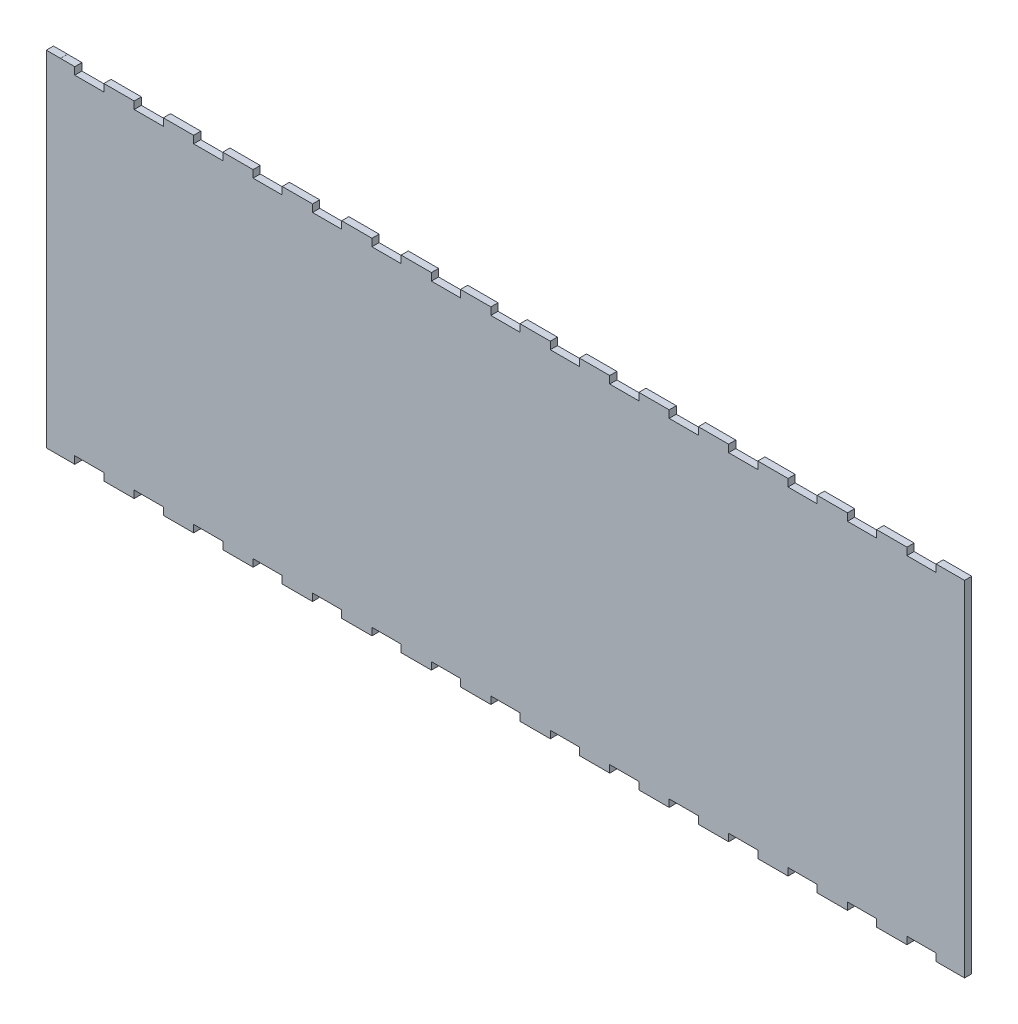
SolidWorks part; units mm, degrees
ref_plane "Front Plane" through (0, 0, 0) normal (0, 0, 1) x (1, 0, 0)
ref_plane "Top Plane" through (0, 0, 0) normal (0, 1, 0) x (1, 0, 0)
ref_plane "Right Plane" through (0, 0, 0) normal (1, 0, 0) x (0, 0, -1)
sketch "Sketch1" plane through (0, 0, 0) normal (0, 0, 1) x (1, 0, 0)
  line L252 (393.8, 152.4) -> (393.8, 149.125)
  line L253 (393.8, 149.125) -> (380.9, 149.125)
  line L254 (380.9, 149.125) -> (380.9, 152.4)
  line L255 (380.9, 152.4) -> (367.4929, 152.4)
  line L256 (367.4929, 152.4) -> (367.4929, 149.125)
  line L257 (367.4929, 149.125) -> (354.5929, 149.125)
  line L258 (354.5929, 149.125) -> (354.5929, 152.4)
  line L259 (354.5929, 152.4) -> (341.1857, 152.4)
  line L260 (341.1857, 152.4) -> (341.1857, 149.125)
  line L261 (341.1857, 149.125) -> (328.2857, 149.125)
  line L262 (328.2857, 149.125) -> (328.2857, 152.4)
  line L263 (328.2857, 152.4) -> (314.8786, 152.4)
  line L264 (314.8786, 152.4) -> (314.8786, 149.125)
  line L265 (314.8786, 149.125) -> (301.9786, 149.125)
  line L266 (301.9786, 149.125) -> (301.9786, 152.4)
  line L267 (301.9786, 152.4) -> (288.5714, 152.4)
  line L268 (288.5714, 152.4) -> (288.5714, 149.125)
  line L269 (288.5714, 149.125) -> (275.6714, 149.125)
  line L270 (275.6714, 149.125) -> (275.6714, 152.4)
  line L271 (275.6714, 152.4) -> (262.2643, 152.4)
  line L272 (262.2643, 152.4) -> (262.2643, 149.125)
  line L273 (262.2643, 149.125) -> (249.3643, 149.125)
  line L274 (249.3643, 149.125) -> (249.3643, 152.4)
  line L275 (249.3643, 152.4) -> (235.9571, 152.4)
  line L276 (235.9571, 152.4) -> (235.9571, 149.125)
  line L277 (235.9571, 149.125) -> (223.0571, 149.125)
  line L278 (223.0571, 149.125) -> (223.0571, 152.4)
  line L279 (223.0571, 152.4) -> (209.65, 152.4)
  line L280 (209.65, 152.4) -> (209.65, 149.125)
  line L281 (209.65, 149.125) -> (196.75, 149.125)
  line L282 (196.75, 149.125) -> (196.75, 152.4)
  line L283 (196.75, 152.4) -> (183.3429, 152.4)
  line L284 (183.3429, 152.4) -> (183.3429, 149.125)
  line L285 (183.3429, 149.125) -> (170.4429, 149.125)
  line L286 (170.4429, 149.125) -> (170.4429, 152.4)
  line L287 (170.4429, 152.4) -> (157.0357, 152.4)
  line L288 (157.0357, 152.4) -> (157.0357, 149.125)
  line L289 (157.0357, 149.125) -> (144.1357, 149.125)
  line L290 (144.1357, 149.125) -> (144.1357, 152.4)
  line L291 (144.1357, 152.4) -> (130.7286, 152.4)
  line L292 (130.7286, 152.4) -> (130.7286, 149.125)
  line L293 (130.7286, 149.125) -> (117.8286, 149.125)
  line L294 (117.8286, 149.125) -> (117.8286, 152.4)
  line L295 (117.8286, 152.4) -> (104.4214, 152.4)
  line L296 (104.4214, 152.4) -> (104.4214, 149.125)
  line L297 (104.4214, 149.125) -> (91.5214, 149.125)
  line L298 (91.5214, 149.125) -> (91.5214, 152.4)
  line L299 (91.5214, 152.4) -> (78.1143, 152.4)
  line L300 (78.1143, 152.4) -> (78.1143, 149.125)
  line L301 (78.1143, 149.125) -> (65.2143, 149.125)
  line L302 (65.2143, 149.125) -> (65.2143, 152.4)
  line L303 (65.2143, 152.4) -> (51.8071, 152.4)
  line L304 (51.8071, 152.4) -> (51.8071, 149.125)
  line L305 (51.8071, 149.125) -> (38.9071, 149.125)
  line L306 (38.9071, 149.125) -> (38.9071, 152.4)
  line L307 (38.9071, 152.4) -> (25.5, 152.4)
  line L308 (25.5, 152.4) -> (25.5, 149.125)
  line L309 (25.5, 149.125) -> (12.6, 149.125)
  line L310 (12.6, 149.125) -> (12.6, 152.4)
  line L311 (12.6, 152.4) -> (6.25, 152.4)
  line L312 (6.25, 152.4) -> (6.25, 152.4254)
  line L313 (6.25, 152.4254) -> (0, 152.4254)
  line L314 (0, 152.4254) -> (0, -0.0254)
  line L315 (0, -0.0254) -> (12.6, -0.0254)
  line L316 (12.6, -0.0254) -> (12.6, 3.275)
  line L317 (12.6, 3.275) -> (25.5, 3.275)
  line L318 (25.5, 3.275) -> (25.5, 0)
  line L319 (25.5, 0) -> (38.9071, 0)
  line L320 (38.9071, 0) -> (38.9071, 3.275)
  line L321 (38.9071, 3.275) -> (51.8071, 3.275)
  line L322 (51.8071, 3.275) -> (51.8071, 0)
  line L323 (51.8071, 0) -> (65.2143, 0)
  line L324 (65.2143, 0) -> (65.2143, 3.275)
  line L325 (65.2143, 3.275) -> (78.1143, 3.275)
  line L326 (78.1143, 3.275) -> (78.1143, 0)
  line L327 (78.1143, 0) -> (91.5214, 0)
  line L328 (91.5214, 0) -> (91.5214, 3.275)
  line L329 (91.5214, 3.275) -> (104.4214, 3.275)
  line L330 (104.4214, 3.275) -> (104.4214, 0)
  line L331 (104.4214, 0) -> (117.8286, 0)
  line L332 (117.8286, 0) -> (117.8286, 3.275)
  line L333 (117.8286, 3.275) -> (130.7286, 3.275)
  line L334 (130.7286, 3.275) -> (130.7286, 0)
  line L335 (130.7286, 0) -> (144.1357, 0)
  line L336 (144.1357, 0) -> (144.1357, 3.275)
  line L337 (144.1357, 3.275) -> (157.0357, 3.275)
  line L338 (157.0357, 3.275) -> (157.0357, 0)
  line L339 (157.0357, 0) -> (170.4429, 0)
  line L340 (170.4429, 0) -> (170.4429, 3.275)
  line L341 (170.4429, 3.275) -> (183.3429, 3.275)
  line L342 (183.3429, 3.275) -> (183.3429, 0)
  line L343 (183.3429, 0) -> (196.75, 0)
  line L344 (196.75, 0) -> (196.75, 3.275)
  line L345 (196.75, 3.275) -> (209.65, 3.275)
  line L346 (209.65, 3.275) -> (209.65, 0)
  line L347 (209.65, 0) -> (223.0571, 0)
  line L348 (223.0571, 0) -> (223.0571, 3.275)
  line L349 (223.0571, 3.275) -> (235.9571, 3.275)
  line L350 (235.9571, 3.275) -> (235.9571, 0)
  line L351 (235.9571, 0) -> (249.3643, 0)
  line L352 (249.3643, 0) -> (249.3643, 3.275)
  line L353 (249.3643, 3.275) -> (262.2643, 3.275)
  line L354 (262.2643, 3.275) -> (262.2643, 0)
  line L355 (262.2643, 0) -> (275.6714, 0)
  line L356 (275.6714, 0) -> (275.6714, 3.275)
  line L357 (275.6714, 3.275) -> (288.5714, 3.275)
  line L358 (288.5714, 3.275) -> (288.5714, 0)
  line L359 (288.5714, 0) -> (301.9786, 0)
  line L360 (301.9786, 0) -> (301.9786, 3.275)
  line L361 (301.9786, 3.275) -> (314.8786, 3.275)
  line L362 (314.8786, 3.275) -> (314.8786, 0)
  line L363 (314.8786, 0) -> (328.2857, 0)
  line L364 (328.2857, 0) -> (328.2857, 3.275)
  line L365 (328.2857, 3.275) -> (341.1857, 3.275)
  line L366 (341.1857, 3.275) -> (341.1857, 0)
  line L367 (341.1857, 0) -> (354.5929, 0)
  line L368 (354.5929, 0) -> (354.5929, 3.275)
  line L369 (354.5929, 3.275) -> (367.4929, 3.275)
  line L370 (367.4929, 3.275) -> (367.4929, 0)
  line L371 (367.4929, 0) -> (380.9, 0)
  line L372 (380.9, 0) -> (380.9, 3.275)
  line L373 (380.9, 3.275) -> (393.8, 3.275)
  line L374 (393.8, 3.275) -> (393.8, 0)
  line L375 (393.8, 0) -> (406.4, 0)
  line L376 (406.4, 0) -> (406.4, 152.4)
  line L377 (406.4, 152.4) -> (393.8, 152.4)
extrude "Boss-Extrude2" add sketch "Sketch1" along normal blind 3.175 contours L314 L315 L316 L317 L318 L319 L320 L321 L322 L323 L324 L325 L326 L327 L328 L329 L330 L331 L332 L333 L334 L335 L336 L337 L338 L339 L340 L341 L342 L343 L344 L345 L346 L347 L348 L349 L350 L351 L352 L353 L354 L355 L356 L357 L358 L359 L360 L361 L362 L363 L364 L365 L366 L367 L368 L369 L370 L371 L372 L373 L374 L375 L376 L377 L252 L253 L254 L255 L256 L257 L258 L259 L260 L261 L262 L263 L264 L265 L266 L267 L268 L269 L270 L271 L272 L273 L274 L275 L276 L277 L278 L279 L280 L281 L282 L283 L284 L285 L286 L287 L288 L289 L290 L291 L292 L293 L294 L295 L296 L297 L298 L299 L300 L301 L302 L303 L304 L305 L306 L307 L308 L309 L310 L311 L312 L313
sketch "DXF" plane through (0, 0, 3.175) normal (0, 0, 1) x (1, 0, 0)
  line L252 (6.3516, 152.527) -> (-0.1016, 152.527)
  line L253 (-0.1016, 152.527) -> (-0.1016, -0.127)
  line L254 (-0.1016, -0.127) -> (12.7016, -0.127)
  line L255 (12.7016, -0.127) -> (12.7016, 3.1734)
  line L256 (12.7016, 3.1734) -> (25.3984, 3.1734)
  line L257 (25.3984, 3.1734) -> (25.3984, -0.1016)
  line L258 (25.3984, -0.1016) -> (39.0087, -0.1016)
  line L259 (39.0087, -0.1016) -> (39.0087, 3.1734)
  line L260 (39.0087, 3.1734) -> (51.7055, 3.1734)
  line L261 (51.7055, 3.1734) -> (51.7055, -0.1016)
  line L262 (51.7055, -0.1016) -> (65.3159, -0.1016)
  line L263 (65.3159, -0.1016) -> (65.3159, 3.1734)
  line L264 (65.3159, 3.1734) -> (78.0127, 3.1734)
  line L265 (78.0127, 3.1734) -> (78.0127, -0.1016)
  line L266 (78.0127, -0.1016) -> (91.623, -0.1016)
  line L267 (91.623, -0.1016) -> (91.623, 3.1734)
  line L268 (91.623, 3.1734) -> (104.3198, 3.1734)
  line L269 (104.3198, 3.1734) -> (104.3198, -0.1016)
  line L270 (104.3198, -0.1016) -> (117.9302, -0.1016)
  line L271 (117.9302, -0.1016) -> (117.9302, 3.1734)
  line L272 (117.9302, 3.1734) -> (130.627, 3.1734)
  line L273 (130.627, 3.1734) -> (130.627, -0.1016)
  line L274 (130.627, -0.1016) -> (144.2373, -0.1016)
  line L275 (144.2373, -0.1016) -> (144.2373, 3.1734)
  line L276 (144.2373, 3.1734) -> (156.9341, 3.1734)
  line L277 (156.9341, 3.1734) -> (156.9341, -0.1016)
  line L278 (156.9341, -0.1016) -> (170.5445, -0.1016)
  line L279 (170.5445, -0.1016) -> (170.5445, 3.1734)
  line L280 (170.5445, 3.1734) -> (183.2413, 3.1734)
  line L281 (183.2413, 3.1734) -> (183.2413, -0.1016)
  line L282 (183.2413, -0.1016) -> (196.8516, -0.1016)
  line L283 (196.8516, -0.1016) -> (196.8516, 3.1734)
  line L284 (196.8516, 3.1734) -> (209.5484, 3.1734)
  line L285 (209.5484, 3.1734) -> (209.5484, -0.1016)
  line L286 (209.5484, -0.1016) -> (223.1587, -0.1016)
  line L287 (223.1587, -0.1016) -> (223.1587, 3.1734)
  line L288 (223.1587, 3.1734) -> (235.8555, 3.1734)
  line L289 (235.8555, 3.1734) -> (235.8555, -0.1016)
  line L290 (235.8555, -0.1016) -> (249.4659, -0.1016)
  line L291 (249.4659, -0.1016) -> (249.4659, 3.1734)
  line L292 (249.4659, 3.1734) -> (262.1627, 3.1734)
  line L293 (262.1627, 3.1734) -> (262.1627, -0.1016)
  line L294 (262.1627, -0.1016) -> (275.773, -0.1016)
  line L295 (275.773, -0.1016) -> (275.773, 3.1734)
  line L296 (275.773, 3.1734) -> (288.4698, 3.1734)
  line L297 (288.4698, 3.1734) -> (288.4698, -0.1016)
  line L298 (288.4698, -0.1016) -> (302.0802, -0.1016)
  line L299 (302.0802, -0.1016) -> (302.0802, 3.1734)
  line L300 (302.0802, 3.1734) -> (314.777, 3.1734)
  line L301 (314.777, 3.1734) -> (314.777, -0.1016)
  line L302 (314.777, -0.1016) -> (328.3873, -0.1016)
  line L303 (328.3873, -0.1016) -> (328.3873, 3.1734)
  line L304 (328.3873, 3.1734) -> (341.0841, 3.1734)
  line L305 (341.0841, 3.1734) -> (341.0841, -0.1016)
  line L306 (341.0841, -0.1016) -> (354.6945, -0.1016)
  line L307 (354.6945, -0.1016) -> (354.6945, 3.1734)
  line L308 (354.6945, 3.1734) -> (367.3913, 3.1734)
  line L309 (367.3913, 3.1734) -> (367.3913, -0.1016)
  line L310 (367.3913, -0.1016) -> (381.0016, -0.1016)
  line L311 (381.0016, -0.1016) -> (381.0016, 3.1734)
  line L312 (381.0016, 3.1734) -> (393.6984, 3.1734)
  line L313 (393.6984, 3.1734) -> (393.6984, -0.1016)
  line L314 (393.6984, -0.1016) -> (406.5016, -0.1016)
  line L315 (406.5016, -0.1016) -> (406.5016, 152.5016)
  line L316 (406.5016, 152.5016) -> (393.6984, 152.5016)
  line L317 (393.6984, 152.5016) -> (393.6984, 149.2266)
  line L318 (393.6984, 149.2266) -> (381.0016, 149.2266)
  line L319 (381.0016, 149.2266) -> (381.0016, 152.5016)
  line L320 (381.0016, 152.5016) -> (367.3913, 152.5016)
  line L321 (367.3913, 152.5016) -> (367.3913, 149.2266)
  line L322 (367.3913, 149.2266) -> (354.6945, 149.2266)
  line L323 (354.6945, 149.2266) -> (354.6945, 152.5016)
  line L324 (354.6945, 152.5016) -> (341.0841, 152.5016)
  line L325 (341.0841, 152.5016) -> (341.0841, 149.2266)
  line L326 (341.0841, 149.2266) -> (328.3873, 149.2266)
  line L327 (328.3873, 149.2266) -> (328.3873, 152.5016)
  line L328 (328.3873, 152.5016) -> (314.777, 152.5016)
  line L329 (314.777, 152.5016) -> (314.777, 149.2266)
  line L330 (314.777, 149.2266) -> (302.0802, 149.2266)
  line L331 (302.0802, 149.2266) -> (302.0802, 152.5016)
  line L332 (302.0802, 152.5016) -> (288.4698, 152.5016)
  line L333 (288.4698, 152.5016) -> (288.4698, 149.2266)
  line L334 (288.4698, 149.2266) -> (275.773, 149.2266)
  line L335 (275.773, 149.2266) -> (275.773, 152.5016)
  line L336 (275.773, 152.5016) -> (262.1627, 152.5016)
  line L337 (262.1627, 152.5016) -> (262.1627, 149.2266)
  line L338 (262.1627, 149.2266) -> (249.4659, 149.2266)
  line L339 (249.4659, 149.2266) -> (249.4659, 152.5016)
  line L340 (249.4659, 152.5016) -> (235.8555, 152.5016)
  line L341 (235.8555, 152.5016) -> (235.8555, 149.2266)
  line L342 (235.8555, 149.2266) -> (223.1587, 149.2266)
  line L343 (223.1587, 149.2266) -> (223.1587, 152.5016)
  line L344 (223.1587, 152.5016) -> (209.5484, 152.5016)
  line L345 (209.5484, 152.5016) -> (209.5484, 149.2266)
  line L346 (209.5484, 149.2266) -> (196.8516, 149.2266)
  line L347 (196.8516, 149.2266) -> (196.8516, 152.5016)
  line L348 (196.8516, 152.5016) -> (183.2413, 152.5016)
  line L349 (183.2413, 152.5016) -> (183.2413, 149.2266)
  line L350 (183.2413, 149.2266) -> (170.5445, 149.2266)
  line L351 (170.5445, 149.2266) -> (170.5445, 152.5016)
  line L352 (170.5445, 152.5016) -> (156.9341, 152.5016)
  line L353 (156.9341, 152.5016) -> (156.9341, 149.2266)
  line L354 (156.9341, 149.2266) -> (144.2373, 149.2266)
  line L355 (144.2373, 149.2266) -> (144.2373, 152.5016)
  line L356 (144.2373, 152.5016) -> (130.627, 152.5016)
  line L357 (130.627, 152.5016) -> (130.627, 149.2266)
  line L358 (130.627, 149.2266) -> (117.9302, 149.2266)
  line L359 (117.9302, 149.2266) -> (117.9302, 152.5016)
  line L360 (117.9302, 152.5016) -> (104.3198, 152.5016)
  line L361 (104.3198, 152.5016) -> (104.3198, 149.2266)
  line L362 (104.3198, 149.2266) -> (91.623, 149.2266)
  line L363 (91.623, 149.2266) -> (91.623, 152.5016)
  line L364 (91.623, 152.5016) -> (78.0127, 152.5016)
  line L365 (78.0127, 152.5016) -> (78.0127, 149.2266)
  line L366 (78.0127, 149.2266) -> (65.3159, 149.2266)
  line L367 (65.3159, 149.2266) -> (65.3159, 152.5016)
  line L368 (65.3159, 152.5016) -> (51.7055, 152.5016)
  line L369 (51.7055, 152.5016) -> (51.7055, 149.2266)
  line L370 (51.7055, 149.2266) -> (39.0087, 149.2266)
  line L371 (39.0087, 149.2266) -> (39.0087, 152.5016)
  line L372 (39.0087, 152.5016) -> (25.3984, 152.5016)
  line L373 (25.3984, 152.5016) -> (25.3984, 149.2266)
  line L374 (25.3984, 149.2266) -> (12.7016, 149.2266)
  line L375 (12.7016, 149.2266) -> (12.7016, 152.5016)
  line L376 (12.7016, 152.5016) -> (6.3516, 152.5016)
  line L377 (6.3516, 152.5016) -> (6.3516, 152.527)
  line L378 (6.3516, 152.527) -> (-0.1016, 152.527)
  line L379 (-0.1016, 152.527) -> (-0.1016, -0.127)
  line L380 (-0.1016, -0.127) -> (12.7016, -0.127)
  line L381 (12.7016, -0.127) -> (12.7016, 3.1734)
  line L382 (12.7016, 3.1734) -> (25.3984, 3.1734)
  line L383 (25.3984, 3.1734) -> (25.3984, -0.1016)
  line L384 (25.3984, -0.1016) -> (39.0087, -0.1016)
  line L385 (39.0087, -0.1016) -> (39.0087, 3.1734)
  line L386 (39.0087, 3.1734) -> (51.7055, 3.1734)
  line L387 (51.7055, 3.1734) -> (51.7055, -0.1016)
  line L388 (51.7055, -0.1016) -> (65.3159, -0.1016)
  line L389 (65.3159, -0.1016) -> (65.3159, 3.1734)
  line L390 (65.3159, 3.1734) -> (78.0127, 3.1734)
  line L391 (78.0127, 3.1734) -> (78.0127, -0.1016)
  line L392 (78.0127, -0.1016) -> (91.623, -0.1016)
  line L393 (91.623, -0.1016) -> (91.623, 3.1734)
  line L394 (91.623, 3.1734) -> (104.3198, 3.1734)
  line L395 (104.3198, 3.1734) -> (104.3198, -0.1016)
  line L396 (104.3198, -0.1016) -> (117.9302, -0.1016)
  line L397 (117.9302, -0.1016) -> (117.9302, 3.1734)
  line L398 (117.9302, 3.1734) -> (130.627, 3.1734)
  line L399 (130.627, 3.1734) -> (130.627, -0.1016)
  line L400 (130.627, -0.1016) -> (144.2373, -0.1016)
  line L401 (144.2373, -0.1016) -> (144.2373, 3.1734)
  line L402 (144.2373, 3.1734) -> (156.9341, 3.1734)
  line L403 (156.9341, 3.1734) -> (156.9341, -0.1016)
  line L404 (156.9341, -0.1016) -> (170.5445, -0.1016)
  line L405 (170.5445, -0.1016) -> (170.5445, 3.1734)
  line L406 (170.5445, 3.1734) -> (183.2413, 3.1734)
  line L407 (183.2413, 3.1734) -> (183.2413, -0.1016)
  line L408 (183.2413, -0.1016) -> (196.8516, -0.1016)
  line L409 (196.8516, -0.1016) -> (196.8516, 3.1734)
  line L410 (196.8516, 3.1734) -> (209.5484, 3.1734)
  line L411 (209.5484, 3.1734) -> (209.5484, -0.1016)
  line L412 (209.5484, -0.1016) -> (223.1587, -0.1016)
  line L413 (223.1587, -0.1016) -> (223.1587, 3.1734)
  line L414 (223.1587, 3.1734) -> (235.8555, 3.1734)
  line L415 (235.8555, 3.1734) -> (235.8555, -0.1016)
  line L416 (235.8555, -0.1016) -> (249.4659, -0.1016)
  line L417 (249.4659, -0.1016) -> (249.4659, 3.1734)
  line L418 (249.4659, 3.1734) -> (262.1627, 3.1734)
  line L419 (262.1627, 3.1734) -> (262.1627, -0.1016)
  line L420 (262.1627, -0.1016) -> (275.773, -0.1016)
  line L421 (275.773, -0.1016) -> (275.773, 3.1734)
  line L422 (275.773, 3.1734) -> (288.4698, 3.1734)
  line L423 (288.4698, 3.1734) -> (288.4698, -0.1016)
  line L424 (288.4698, -0.1016) -> (302.0802, -0.1016)
  line L425 (302.0802, -0.1016) -> (302.0802, 3.1734)
  line L426 (302.0802, 3.1734) -> (314.777, 3.1734)
  line L427 (314.777, 3.1734) -> (314.777, -0.1016)
  line L428 (314.777, -0.1016) -> (328.3873, -0.1016)
  line L429 (328.3873, -0.1016) -> (328.3873, 3.1734)
  line L430 (328.3873, 3.1734) -> (341.0841, 3.1734)
  line L431 (341.0841, 3.1734) -> (341.0841, -0.1016)
  line L432 (341.0841, -0.1016) -> (354.6945, -0.1016)
  line L433 (354.6945, -0.1016) -> (354.6945, 3.1734)
  line L434 (354.6945, 3.1734) -> (367.3913, 3.1734)
  line L435 (367.3913, 3.1734) -> (367.3913, -0.1016)
  line L436 (367.3913, -0.1016) -> (381.0016, -0.1016)
  line L437 (381.0016, -0.1016) -> (381.0016, 3.1734)
  line L438 (381.0016, 3.1734) -> (393.6984, 3.1734)
  line L439 (393.6984, 3.1734) -> (393.6984, -0.1016)
  line L440 (393.6984, -0.1016) -> (406.5016, -0.1016)
  line L441 (406.5016, -0.1016) -> (406.5016, 152.5016)
  line L442 (406.5016, 152.5016) -> (393.6984, 152.5016)
  line L443 (393.6984, 152.5016) -> (393.6984, 149.2266)
  line L444 (393.6984, 149.2266) -> (381.0016, 149.2266)
  line L445 (381.0016, 149.2266) -> (381.0016, 152.5016)
  line L446 (381.0016, 152.5016) -> (367.3913, 152.5016)
  line L447 (367.3913, 152.5016) -> (367.3913, 149.2266)
  line L448 (367.3913, 149.2266) -> (354.6945, 149.2266)
  line L449 (354.6945, 149.2266) -> (354.6945, 152.5016)
  line L450 (354.6945, 152.5016) -> (341.0841, 152.5016)
  line L451 (341.0841, 152.5016) -> (341.0841, 149.2266)
  line L452 (341.0841, 149.2266) -> (328.3873, 149.2266)
  line L453 (328.3873, 149.2266) -> (328.3873, 152.5016)
  line L454 (328.3873, 152.5016) -> (314.777, 152.5016)
  line L455 (314.777, 152.5016) -> (314.777, 149.2266)
  line L456 (314.777, 149.2266) -> (302.0802, 149.2266)
  line L457 (302.0802, 149.2266) -> (302.0802, 152.5016)
  line L458 (302.0802, 152.5016) -> (288.4698, 152.5016)
  line L459 (288.4698, 152.5016) -> (288.4698, 149.2266)
  line L460 (288.4698, 149.2266) -> (275.773, 149.2266)
  line L461 (275.773, 149.2266) -> (275.773, 152.5016)
  line L462 (275.773, 152.5016) -> (262.1627, 152.5016)
  line L463 (262.1627, 152.5016) -> (262.1627, 149.2266)
  line L464 (262.1627, 149.2266) -> (249.4659, 149.2266)
  line L465 (249.4659, 149.2266) -> (249.4659, 152.5016)
  line L466 (249.4659, 152.5016) -> (235.8555, 152.5016)
  line L467 (235.8555, 152.5016) -> (235.8555, 149.2266)
  line L468 (235.8555, 149.2266) -> (223.1587, 149.2266)
  line L469 (223.1587, 149.2266) -> (223.1587, 152.5016)
  line L470 (223.1587, 152.5016) -> (209.5484, 152.5016)
  line L471 (209.5484, 152.5016) -> (209.5484, 149.2266)
  line L472 (209.5484, 149.2266) -> (196.8516, 149.2266)
  line L473 (196.8516, 149.2266) -> (196.8516, 152.5016)
  line L474 (196.8516, 152.5016) -> (183.2413, 152.5016)
  line L475 (183.2413, 152.5016) -> (183.2413, 149.2266)
  line L476 (183.2413, 149.2266) -> (170.5445, 149.2266)
  line L477 (170.5445, 149.2266) -> (170.5445, 152.5016)
  line L478 (170.5445, 152.5016) -> (156.9341, 152.5016)
  line L479 (156.9341, 152.5016) -> (156.9341, 149.2266)
  line L480 (156.9341, 149.2266) -> (144.2373, 149.2266)
  line L481 (144.2373, 149.2266) -> (144.2373, 152.5016)
  line L482 (144.2373, 152.5016) -> (130.627, 152.5016)
  line L483 (130.627, 152.5016) -> (130.627, 149.2266)
  line L484 (130.627, 149.2266) -> (117.9302, 149.2266)
  line L485 (117.9302, 149.2266) -> (117.9302, 152.5016)
  line L486 (117.9302, 152.5016) -> (104.3198, 152.5016)
  line L487 (104.3198, 152.5016) -> (104.3198, 149.2266)
  line L488 (104.3198, 149.2266) -> (91.623, 149.2266)
  line L489 (91.623, 149.2266) -> (91.623, 152.5016)
  line L490 (91.623, 152.5016) -> (78.0127, 152.5016)
  line L491 (78.0127, 152.5016) -> (78.0127, 149.2266)
  line L492 (78.0127, 149.2266) -> (65.3159, 149.2266)
  line L493 (65.3159, 149.2266) -> (65.3159, 152.5016)
  line L494 (65.3159, 152.5016) -> (51.7055, 152.5016)
  line L495 (51.7055, 152.5016) -> (51.7055, 149.2266)
  line L496 (51.7055, 149.2266) -> (39.0087, 149.2266)
  line L497 (39.0087, 149.2266) -> (39.0087, 152.5016)
  line L498 (39.0087, 152.5016) -> (25.3984, 152.5016)
  line L499 (25.3984, 152.5016) -> (25.3984, 149.2266)
  line L500 (25.3984, 149.2266) -> (12.7016, 149.2266)
  line L501 (12.7016, 149.2266) -> (12.7016, 152.5016)
  line L502 (12.7016, 152.5016) -> (6.3516, 152.5016)
  line L503 (6.3516, 152.5016) -> (6.3516, 152.527)
  dimension "D1" = 0.1016
extrude "DXF-Extrude" [suppressed] add sketch "DXF" against normal blind 3.175
